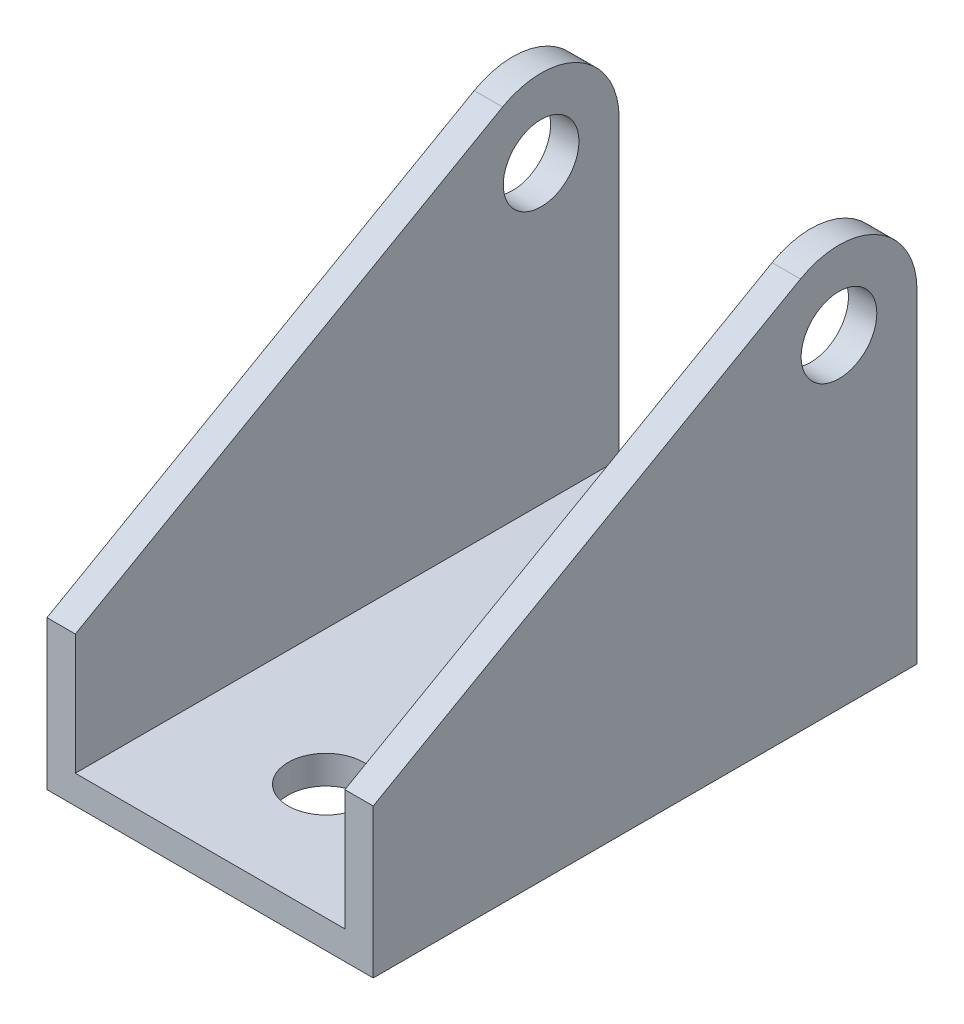
SolidWorks part; units mm, degrees
ref_plane "Front Plane" through (0, 0, 0) normal (0, 0, 1) x (1, 0, 0)
ref_plane "Top Plane" through (0, 0, 0) normal (0, 1, 0) x (1, 0, 0)
ref_plane "Right Plane" through (0, 0, 0) normal (1, 0, 0) x (0, 0, -1)
sketch "Sketch1" plane through (0, 0, 0) normal (1, 0, 0) x (0, 0, -1)
  line L0 (0, 16.002) -> (45.8965, 42.0854)
  line L1 (0, 0) -> (58.42, 0)
  line L2 (0, 0) -> (0, 16.002)
  line L4 (58.42, 0) -> (58.42, 34.798)
  arc A0 (58.42, 34.798) -> (45.8965, 42.0854) centre (50.038, 34.798) ccw
  circle A1 centre (50.038, 34.798) radius 4.064
  dimension "D3" = 16.764
  dimension "D2" = 8.128
  dimension "D1" = 58.42
  dimension "D4" = 16.002
extrude "Boss-Extrude1" add sketch "Sketch1" against normal blind 35.052
sketch "Sketch2" plane through (0, 0, 0) normal (0, 0, 1) x (1, 0, 0)
  line L0 (-35.052, 42.0854) -> (-35.052, 16.002) construction
  line L5 (-32.004, 3.048) -> (-3.048, 3.048)
  line L6 (-32.004, 3.048) -> (-32.004, 43.18)
  line L7 (-32.004, 43.18) -> (-3.048, 43.18)
  line L8 (-3.048, 3.048) -> (-3.048, 43.18)
  line L9 (0, 42.0854) -> (0, 16.002) construction
  line L10 (-35.052, 0) -> (0, 0) construction
  line L11 (0, 43.18) -> (-35.052, 43.18) construction
  dimension "D1" = 3.048
  dimension "D2" = 3.048
  dimension "D3" = 3.048
extrude "Cut-Extrude1" cut sketch "Sketch2" against normal through all
sketch "Sketch3" plane through (0, 0, 0) normal (0, 1, 0) x (1, 0, 0)
  line L0 (-32.004, 0) -> (-3.048, 0) construction
  line L1 (-21.844, 43.9302) -> (-21.844, 58.42)
  line L2 (-32.004, 58.42) -> (-3.048, 58.42) construction
  line L3 (-13.208, 43.9302) -> (-13.208, 58.42)
  line L4 (-21.844, 58.42) -> (-13.208, 58.42)
  circle A0 centre (-17.526, 12.446) radius 4.064
  arc A1 (-21.844, 43.9302) -> (-13.208, 43.9302) centre (-17.526, 43.9302) ccw
  dimension "D2" = 8.128
  dimension "D3" = 8.636
  dimension "D1" = 12.446
extrude "Cut-Extrude3" cut sketch "Sketch3" against normal blind 35.052 and the other way through all
